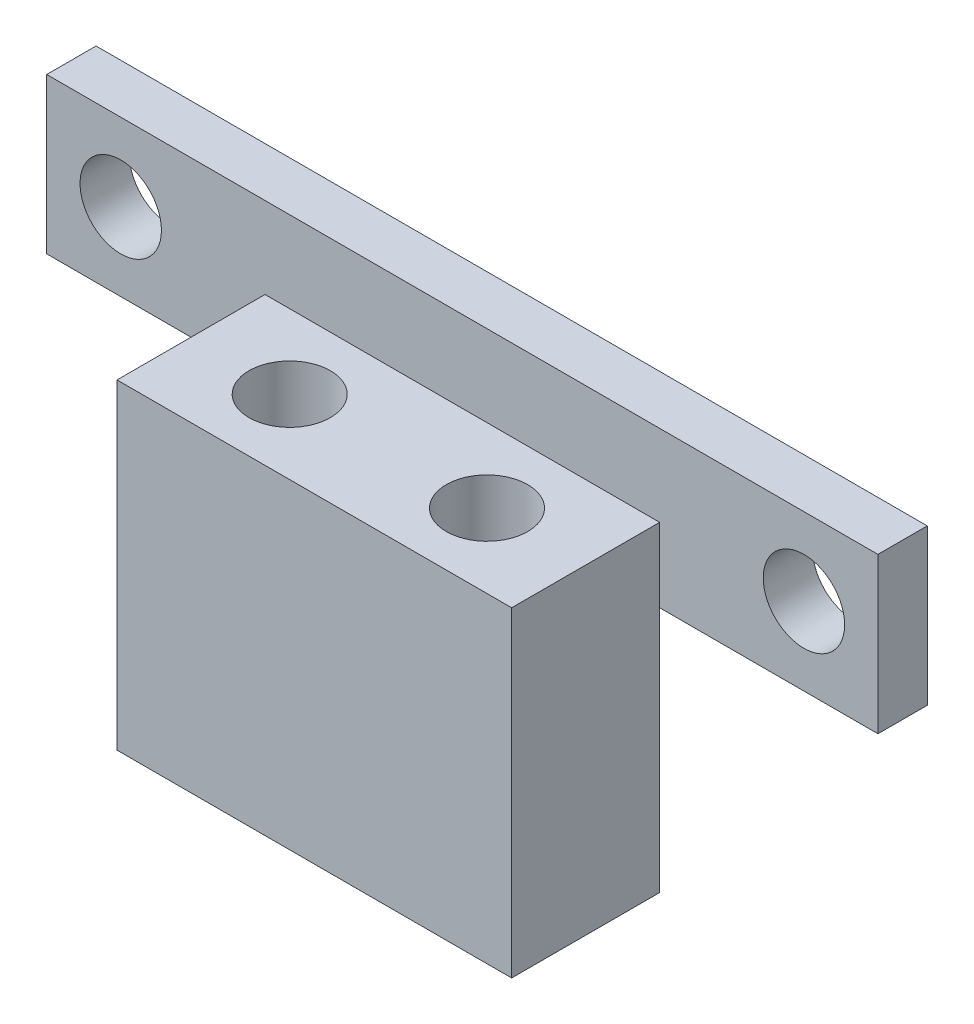
SolidWorks part; units mm, degrees
ref_plane "Front Plane" through (0, 0, 0) normal (0, 0, 1) x (1, 0, 0)
ref_plane "Top Plane" through (0, 0, 0) normal (0, 1, 0) x (1, 0, 0)
ref_plane "Right Plane" through (0, 0, 0) normal (1, 0, 0) x (0, 0, -1)
sketch "Sketch1" plane through (0, 0, 0) normal (0, 0, 1) x (1, 0, 0)
  line L1 (0, 0) -> (33.7, 0)
  line L2 (0, 0) -> (0, 6.3)
  line L3 (0, 6.3) -> (33.7, 6.3)
  line L4 (33.7, 0) -> (33.7, 6.3)
  circle A0 centre (3, 3.15) radius 1.65
  circle A1 centre (30.7, 3.15) radius 1.65
  dimension "D2" = 3.3
  dimension "D3" = 3.15
  dimension "D4" = 3
  dimension "D6" = 3.15
  dimension "D7" = 27.7
  dimension "D1" = 6.3
  dimension "D5" = 3
extrude "Boss-Extrude1" add sketch "Sketch1" along normal blind 2
sketch "Sketch2" plane through (0, 0, 2) normal (0, 0, 1) x (1, 0, 0)
  line L0 (0, 0) -> (33.7, 0) construction
  line L1 (8.85, 0) -> (24.85, 0)
  line L2 (8.85, 0) -> (8.85, 3)
  line L3 (8.85, 3) -> (24.85, 3)
  line L4 (24.85, 0) -> (24.85, 3)
  line L5 (8.85, 0) -> (0, 0) construction
  line L6 (24.85, 0) -> (33.7, 0) construction
  dimension "D1" = 3
  dimension "D2" = 16
extrude "Boss-Extrude2" add sketch "Sketch2" along normal blind 6
sketch "Sketch3" plane through (0, 3, 0) normal (0, 1, 0) x (1, 0, 0)
  line L0 (12.85, -5) -> (8.85, -5) construction
  line L1 (8.85, -8) -> (8.85, -2) construction
  line L2 (20.85, -5) -> (24.85, -5) construction
  line L3 (24.85, -8) -> (24.85, -2) construction
  line L4 (24.85, -8) -> (8.85, -8) construction
  circle A0 centre (12.85, -5) radius 1.65
  circle A1 centre (20.85, -5) radius 1.65
  dimension "D1" = 3.3
  dimension "D2" = 3.3
  dimension "D3" = 8
  dimension "D4" = 3
  dimension "D5" = 3
extrude "Cut-Extrude1" cut sketch "Sketch3" against normal blind 6
sketch "Sketch4" plane through (0, 0, 0) normal (0, -1, 0) x (1, 0, 0)
  line L1 (8.85, 8) -> (24.85, 8)
  line L2 (8.85, 8) -> (8.85, 2)
  line L3 (8.85, 2) -> (24.85, 2)
  line L4 (24.85, 8) -> (24.85, 2)
  circle A0 centre (12.85, 5) radius 1.65
  circle A1 centre (20.85, 5) radius 1.65
extrude "Boss-Extrude3" add sketch "Sketch4" along normal blind 10
